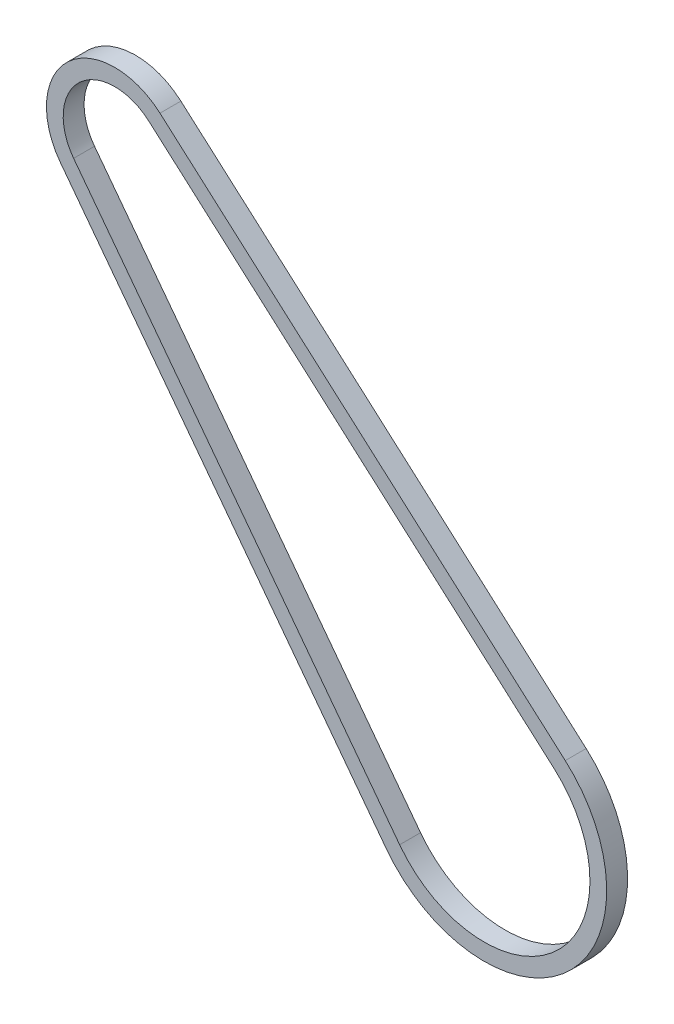
SolidWorks part; units mm, degrees
ref_plane "Front" through (0, 0, 0) normal (0, 0, 1) x (1, 0, 0)
ref_plane "Top" through (0, 0, 0) normal (0, 1, 0) x (1, 0, 0)
ref_plane "Right" through (0, 0, 0) normal (1, 0, 0) x (0, 0, -1)
sketch "Sketch1" plane through (0, 0, 0) normal (0, 0, 1) x (1, 0, 0)
  line L0 (-34.8684, -17.329) -> (-133.9068, 113.7338)
  line L1 (19.4939, 33.0274) -> (-103.6197, 141.7891)
  line L2 (-30.8155, -14.2663) -> (-129.8538, 116.7965)
  line L3 (16.1305, 29.2202) -> (-106.983, 137.982)
  circle A0 centre (-117.355, 126.2413) radius 20.746 construction
  arc A1 (-34.8684, -17.329) -> (19.4939, 33.0274) centre (-5.1597, 5.1206) ccw
  arc A3 (-103.6197, 141.7891) -> (-133.9068, 113.7338) centre (-117.355, 126.2413) ccw
  arc A4 (-106.983, 137.982) -> (-129.8538, 116.7965) centre (-117.355, 126.2413) ccw
  arc A5 (-30.8155, -14.2663) -> (16.1305, 29.2202) centre (-5.1597, 5.1206) ccw
  dimension "D1" = 5.08
extrude "Boss-Extrude1" add sketch "Sketch1" along normal blind 6.35
